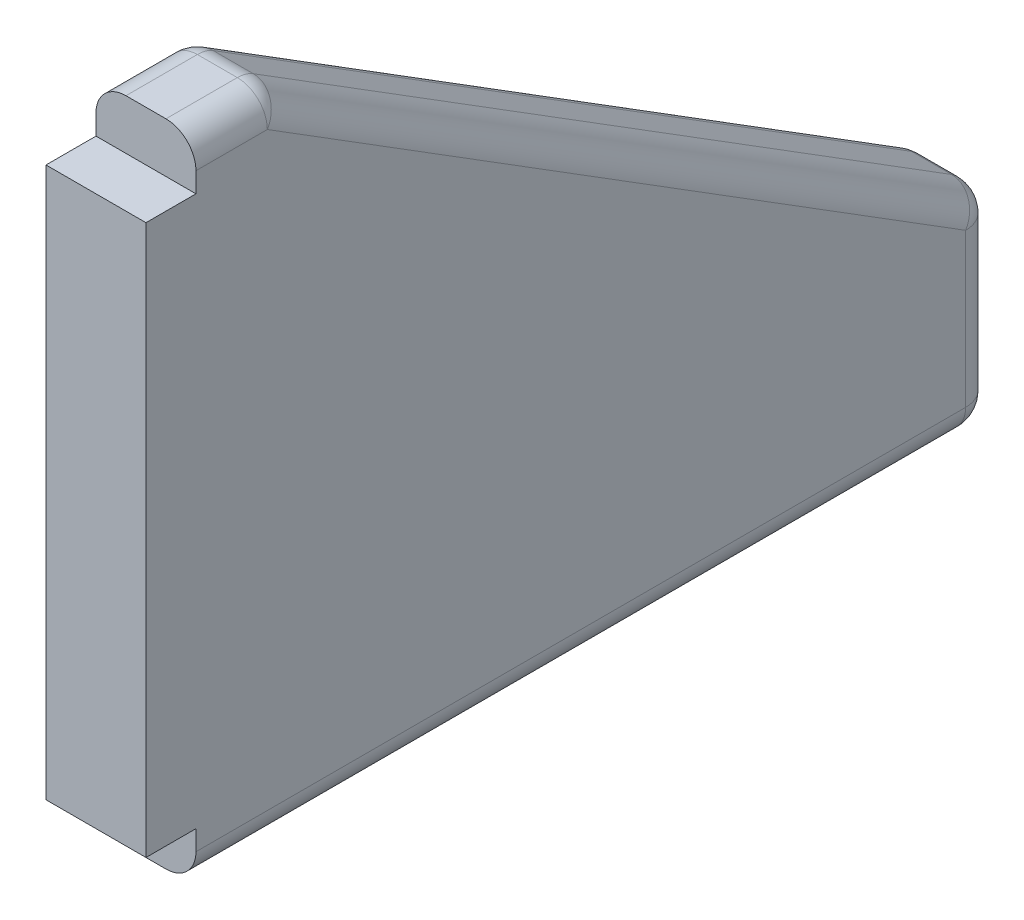
SolidWorks part; units mm, degrees
ref_plane "Front Plane" through (0, 0, 0) normal (0, 0, 1) x (1, 0, 0)
ref_plane "Top Plane" through (0, 0, 0) normal (0, 1, 0) x (1, 0, 0)
ref_plane "Right Plane" through (0, 0, 0) normal (1, 0, 0) x (0, 0, -1)
sketch "Sketch7" plane through (0, 0, 0) normal (1, 0, 0) x (0, 0, -1)
  line L0 (0, 0) -> (0, 5)
  line L1 (0, 0) -> (80, 0) construction
  line L2 (0, 0) -> (0, 5) construction
  line L3 (0, 75.2727) -> (80, 75.2727) construction
  line L4 (80, 0) -> (80, 75.2727) construction
  line L5 (0, 65) -> (8, 65)
  line L6 (8, 65) -> (80, 20)
  line L7 (80, 20) -> (80, 0)
  line L8 (80, 0) -> (0, 0)
  line L9 (0, 60) -> (0, 65)
  line L10 (0, 60) -> (-5, 60)
  line L12 (0, 5) -> (-5, 5)
  line L13 (-5, 60) -> (-5, 5)
  line L14 (0, 60) -> (0, 75.2727) construction
  dimension "D1" = 20
  dimension "D2" = 80
  dimension "D3" = 8
  dimension "D4" = 65
  dimension "D5" = 55
  dimension "D6" = 5
  dimension "D7" = 5
extrude "Boss-Extrude5" add sketch "Sketch7" along normal blind 10
fillet "Fillet1" radius 3 11 edges at (10, 65, -4) (0, 65, -4) (0, 0, -40) (10, 0, -40) (5, 0, -80) (10, 10, -80) (0, 10, -80) (5, 20, -80) (5, 65, -8) (0, 42.5, -44) (10, 42.5, -44)
